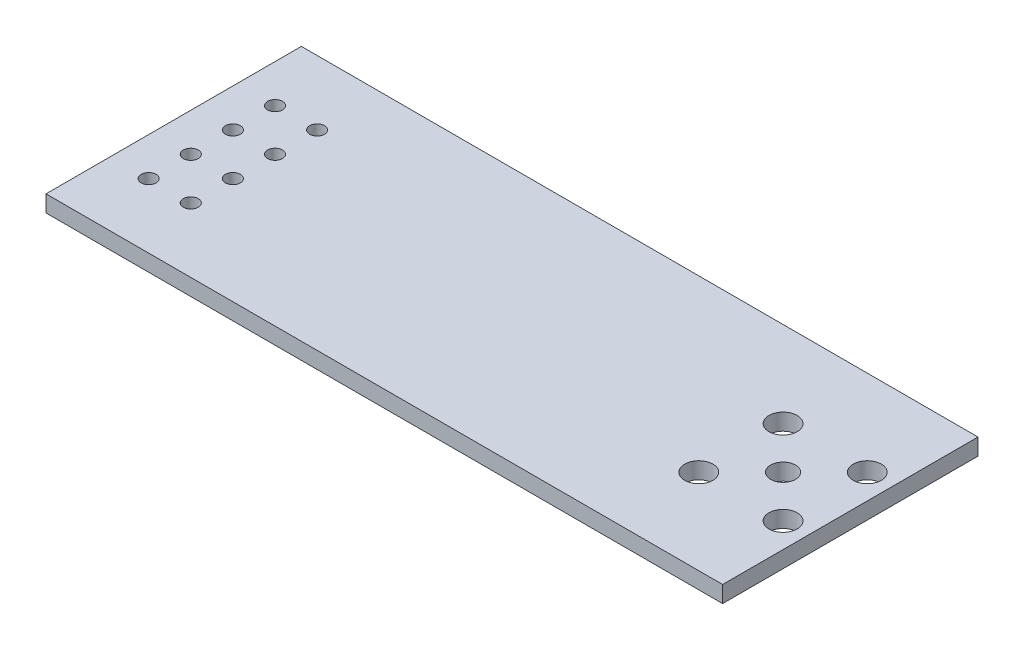
SolidWorks part; units mm, degrees
ref_plane "Спереди" through (0, 0, 0) normal (0, 0, 1) x (1, 0, 0)
ref_plane "Сверху" through (0, 0, 0) normal (0, 1, 0) x (1, 0, 0)
ref_plane "Справа" through (0, 0, 0) normal (1, 0, 0) x (0, 0, -1)
sketch "Эскиз1" plane through (0, 0, 0) normal (0, 1, 0) x (1, 0, 0)
  line L0 (34.22, 5.1444) -> (39.3, 10.2244) construction
  line L1 (0, 0) -> (40.8, 0)
  line L2 (0, 0) -> (0, 15.4)
  line L3 (0, 15.4) -> (40.8, 15.4)
  line L4 (40.8, 0) -> (40.8, 15.4)
  line L5 (39.3, 5.1444) -> (34.22, 10.2244) construction
  circle A0 centre (2.3, 3.89) radius 0.45
  circle A1 centre (2.3, 6.43) radius 0.45
  circle A2 centre (2.3, 8.97) radius 0.45
  circle A3 centre (2.3, 11.51) radius 0.45
  circle A4 centre (4.84, 3.89) radius 0.45
  circle A5 centre (4.84, 6.43) radius 0.45
  circle A6 centre (4.84, 8.97) radius 0.45
  circle A7 centre (4.84, 11.51) radius 0.45
  circle A8 centre (34.22, 5.1444) radius 0.85
  circle A9 centre (34.22, 10.2244) radius 0.85
  circle A10 centre (39.3, 5.1444) radius 0.85
  circle A11 centre (39.3, 10.2244) radius 0.85
  circle A12 centre (36.76, 7.6844) radius 0.75
  dimension "D3" = 0.9
  dimension "D14" = 1.7
  dimension "D18" = 1.5
  dimension "D1" = 15.4
  dimension "D2" = 40.8
  dimension "D4" = 2.54
  dimension "D5" = 2.54
  dimension "D6" = 2.54
  dimension "D7" = 2.54
  dimension "D8" = 2.54
  dimension "D9" = 2.54
  dimension "D10" = 2.54
  dimension "D11" = 3.89
  dimension "D12" = 3.89
  dimension "D13" = 2.3
  dimension "D15" = 5.08
  dimension "D16" = 5.08
  dimension "D17" = 5.08
  dimension "D19" = 1.5
extrude "Бобышка-Вытянуть1" add sketch "Эскиз1" along normal blind 1
